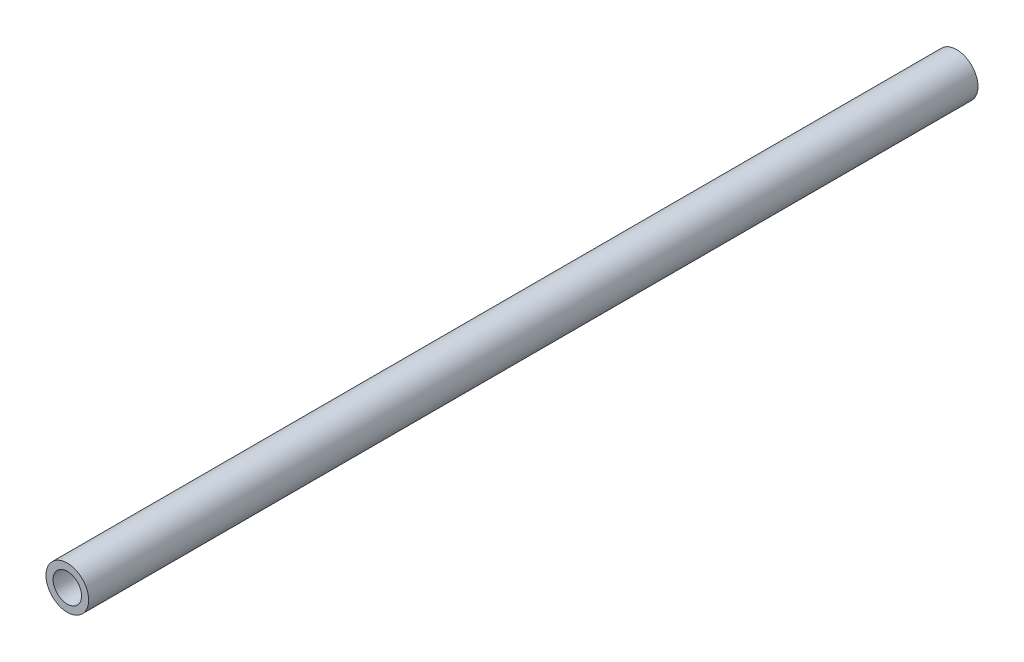
SolidWorks part; units mm, degrees
material "Carbon Fiber Rod"
ref_plane "Front Plane" through (0, 0, 0) normal (0, 0, 1) x (1, 0, 0)
ref_plane "Top Plane" through (0, 0, 0) normal (0, 1, 0) x (1, 0, 0)
ref_plane "Right Plane" through (0, 0, 0) normal (1, 0, 0) x (0, 0, -1)
sketch "Sketch1" plane through (0, 0, 0) normal (0, 0, 1) x (1, 0, 0)
  circle A0 centre (0, 0) radius 3
  circle A1 centre (0, 0) radius 2
  dimension "D1" = 6
  dimension "D2" = 4
extrude "Boss-Extrude1" add sketch "Sketch1" along normal blind 125
